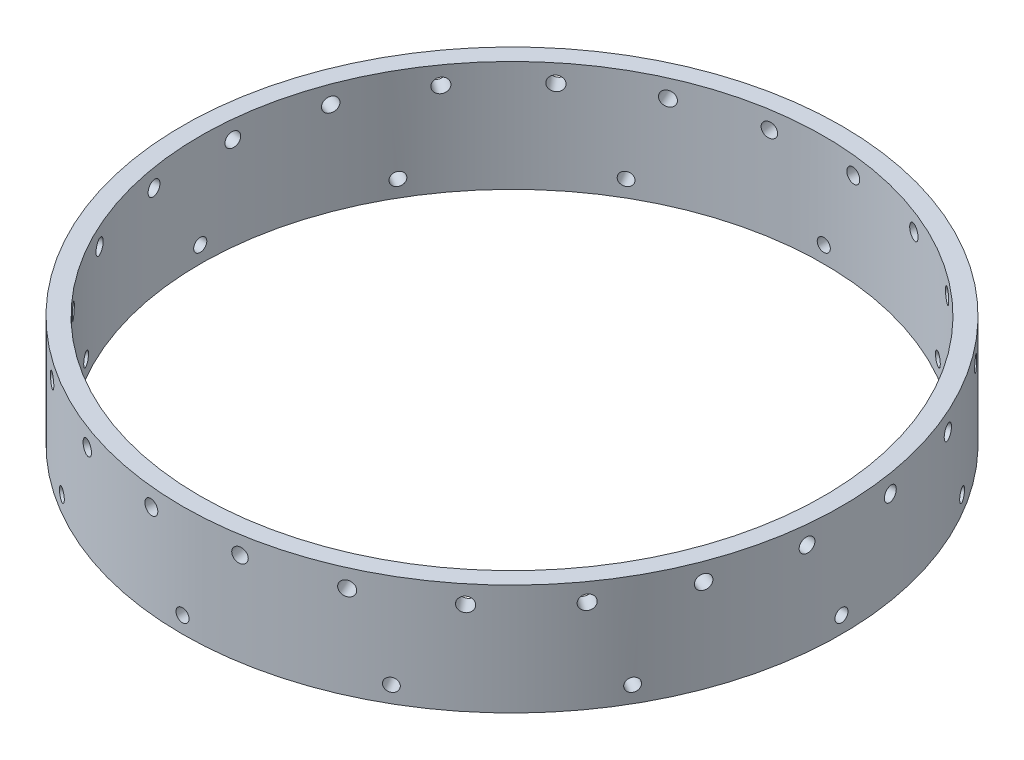
SolidWorks part; units mm, degrees
ref_plane "Front Plane" through (0, 0, 0) normal (0, 0, 1) x (1, 0, 0)
ref_plane "Top Plane" through (0, 0, 0) normal (0, 1, 0) x (1, 0, 0)
ref_plane "Right Plane" through (0, 0, 0) normal (1, 0, 0) x (0, 0, -1)
sketch "Sketch1" plane through (0, 0, 0) normal (0, 1, 0) x (1, 0, 0)
  circle A0 centre (0, 0) radius 75.565
  circle A1 centre (0, 0) radius 71.501
  dimension "D1" = 143.002
  dimension "D2" = 151.13
extrude "Boss-Extrude1" add sketch "Sketch1" along normal blind 25.4
hole_wizard "Tap Drill for M4x0.7 Tap1" positions "3DSketch1" profile "Sketch2" hole size "M4x0.7" standard "ANSI Metric"
sketch3d "3DSketch1"
  point P0 (31.0779, 21.2994, 68.8784)
sketch "Sketch2" plane through (31.0779, 21.2994, 68.8784) normal (0, 1, 0) x (0.9115, 0, -0.4113)
  line L0 (0, 0) -> (0, 157.6666)
  line L1 (0, 157.6666) -> (1.65, 157.6666)
  line L2 (1.65, 157.6666) -> (1.65, 0)
  line L5 (1.65, 0) -> (0, 0)
  line L11 (0, -6.35) -> (0, 107.95) construction
  dimension "Thru Hole Dia." = 3.3
  dimension "Thru Hole Depth" = 157.6666
pattern_circular "CirPattern1" count 24 every 15 about axis through (0, 25.4, 0) along (0, 1, 0) of "Tap Drill for M4x0.7 Tap1"
sketch "Sketch4" plane through (0, 0, 0) normal (1, 0, 0) x (0, 0, -1)
  line L0 (0, 0) -> (0, 3.7846) construction
  circle A0 centre (0, 3.7846) radius 1.5
extrude "Cut-Extrude1" cut sketch "Sketch4" against normal blind 113.03
pattern_circular "CirPattern2" count 12 every 30 about axis through (0, 0, 0) along (0, 1, 0) of "Cut-Extrude1"
